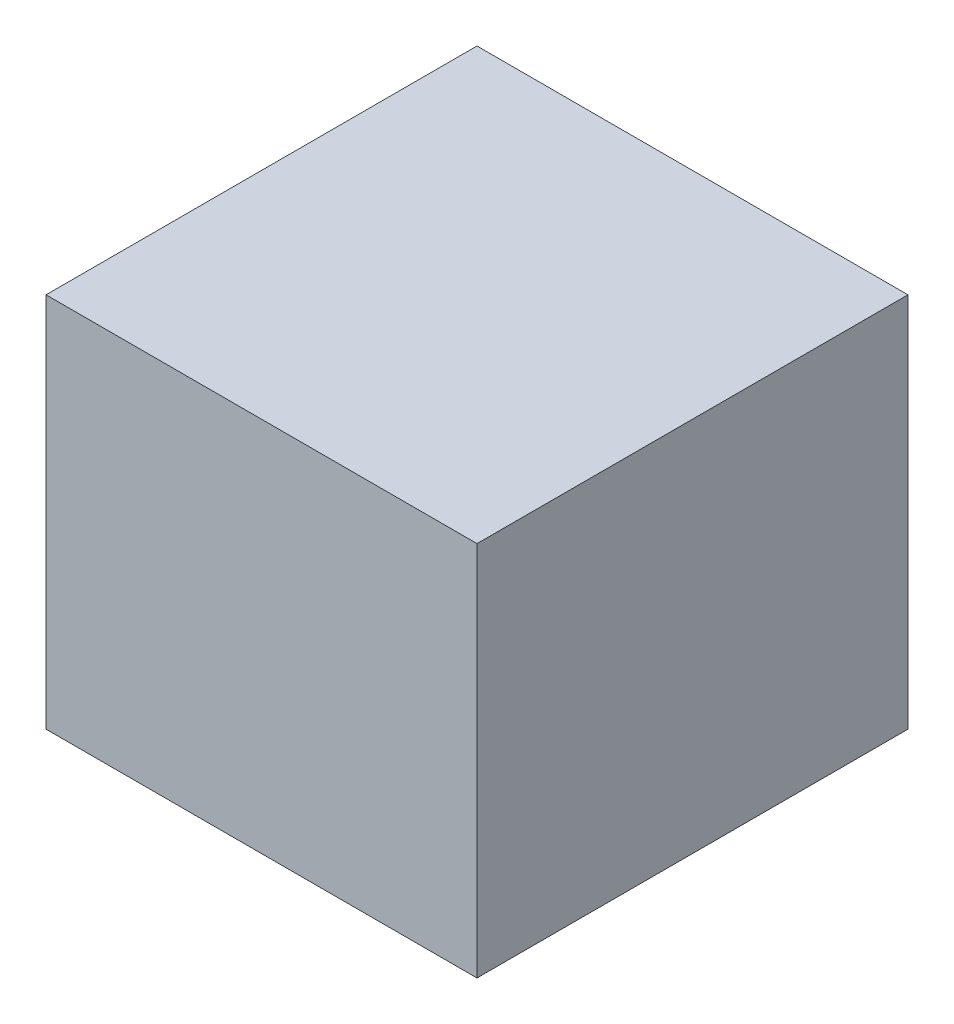
SolidWorks part; units mm, degrees
ref_plane "Front Plane" through (0, 0, 0) normal (0, 0, 1) x (1, 0, 0)
ref_plane "Top Plane" through (0, 0, 0) normal (0, 1, 0) x (1, 0, 0)
ref_plane "Right Plane" through (0, 0, 0) normal (1, 0, 0) x (0, 0, -1)
sketch "Sketch1" plane through (0, 0, 0) normal (0, 1, 0) x (1, 0, 0)
  line L1 (-91.948, -91.948) -> (91.948, -91.948)
  line L2 (-91.948, -91.948) -> (-91.948, 91.948)
  line L3 (-91.948, 91.948) -> (91.948, 91.948)
  line L4 (91.948, -91.948) -> (91.948, 91.948)
  line L5 (-91.948, -91.948) -> (91.948, 91.948) construction
  line L6 (-91.948, 91.948) -> (91.948, -91.948) construction
  point P0 (0, 0)
  dimension "D1" = 183.896
  dimension "D2" = 183.896
extrude "Boss-Extrude1" add sketch "Sketch1" along normal blind 160.528
